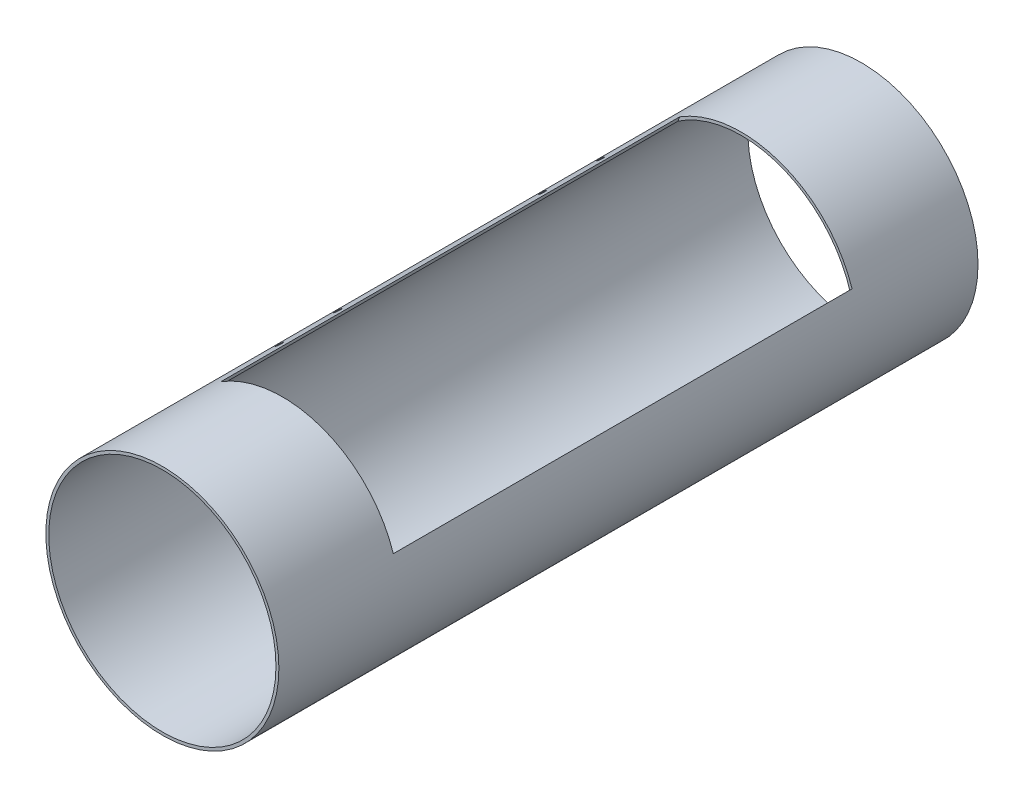
SolidWorks part; units mm, degrees
ref_plane "Front Plane" through (0, 0, 0) normal (0, 0, 1) x (1, 0, 0)
ref_plane "Top Plane" through (0, 0, 0) normal (0, 1, 0) x (1, 0, 0)
ref_plane "Right Plane" through (0, 0, 0) normal (1, 0, 0) x (0, 0, -1)
sketch "Sketch2" plane through (0, 0, 0) normal (0, 0, 1) x (1, 0, 0)
  circle A0 centre (0, 0) radius 49.53
  circle A1 centre (0, 0) radius 50.8
  dimension "D1" = 101.6
  dimension "D2" = 1.27
extrude "Boss-Extrude1" add sketch "Sketch2" along normal blind 304.8
sketch "Sketch6" plane through (0, 0, 0) normal (0, 1, 0) x (1, 0, 0)
  line L0 (0, 0) -> (0, -200.3168)
ref_plane "Plane4" through (0, 0, 0) normal (0.342, 0.9397, 0) x (0, 0, 1)
sketch "Sketch3" plane through (0, 0, 0) normal (0.342, 0.9397, 0) x (0.9397, -0.342, 0)
  line L0 (-50.8, -304.8) -> (50.8, -304.8) construction
  line L1 (-40, -52.4) -> (40, -52.4)
  line L2 (-40, -52.4) -> (-40, -252.4)
  line L3 (-40, -252.4) -> (40, -252.4)
  line L4 (40, -52.4) -> (40, -252.4)
  line L5 (-40, -52.4) -> (40, -252.4) construction
  line L6 (-40, -252.4) -> (40, -52.4) construction
  line L7 (49.53, 0) -> (-49.53, 0) construction
  line L8 (-50.8, -304.8) -> (50.8, -304.8) construction
  line L9 (49.53, 0) -> (-49.53, 0) construction
  line L10 (50.8, -304.8) -> (50.8, 0) construction
  line L11 (50.8, -304.8) -> (50.8, 0) construction
  point P0 (0, -152.4)
  point P15 (50.8, -152.4)
  dimension "D1" = 200
  dimension "D2" = 80
extrude "Cut-Extrude1" cut sketch "Sketch3" along normal up to surface (31.3152 mm away)
ref_plane "Plane1" through (0, 0, 152.4) normal (0, 0, -1) x (-1, 0, 0)
ref_plane "Plane2" through (-49.53, 0, 0) normal (1, 0, 0) x (0, 0, -1)
ref_plane "Plane3" through (-26.3501, 39.2245, 0) normal (0.5576, -0.8301, 0) x (-0.8301, -0.5576, 0)
sketch "Sketch7" plane through (-78.0384, 6.2642, 0) normal (0.6187, -0.7856, 0) x (-0.7856, -0.6187, 0)
  line L0 (-106.9606, -52.4) -> (-61.1986, -52.4) construction
  line L1 (-62.9883, -252.4) -> (-62.9883, -52.4) construction
  line L3 (-106.9606, -52.4) -> (-61.1986, -52.4)
  line L4 (-62.9883, -252.4) -> (-62.9883, -52.4)
  circle A0 centre (-57.4306, -197) radius 1.5
  circle A1 centre (-57.4306, -222.4) radius 1.5
  circle A2 centre (-57.4306, -82.4) radius 1.5
  circle A3 centre (-57.4306, -107.8) radius 1.5
  dimension "D1" = 3
  dimension "D2" = 3
  dimension "D3" = 25.4
  dimension "D4" = 5.5578
  dimension "D5" = 30
  dimension "D6" = 30
  dimension "D7" = 25.4
extrude "Cut-Extrude2" cut sketch "Sketch7" along normal blind 10 contours A1 | A0 | A3 | A2
